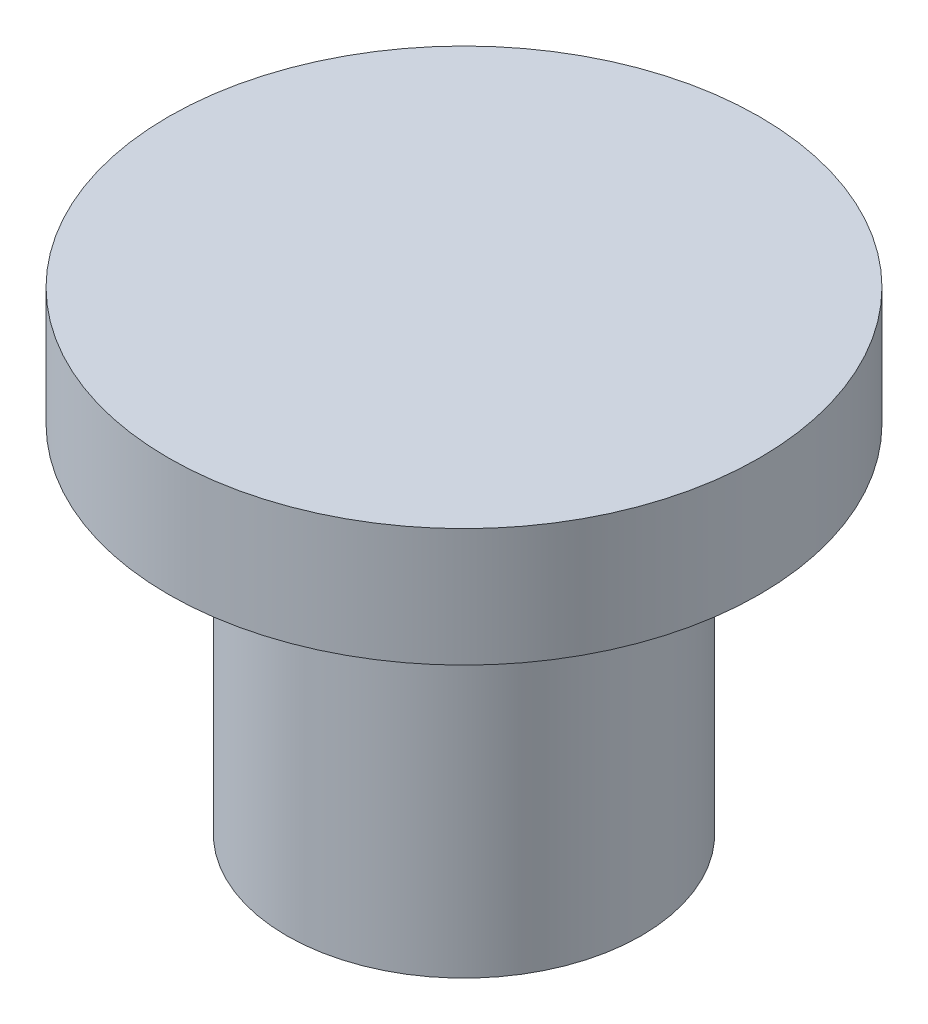
SolidWorks part; units mm, degrees
ref_plane "Спереди" through (0, 0, 0) normal (0, 0, 1) x (1, 0, 0)
ref_plane "Сверху" through (0, 0, 0) normal (0, 1, 0) x (1, 0, 0)
ref_plane "Справа" through (0, 0, 0) normal (1, 0, 0) x (0, 0, -1)
sketch "Эскиз1" plane through (0, 0, 0) normal (0, 0, 1) x (1, 0, 0)
  line L1 (-5, 8) -> (-5, 6)
  line L2 (-5, 6) -> (-3, 6)
  line L3 (-3, 6) -> (-3, 0)
  line L5 (-5, 8) -> (0, 8)
  line L7 (-3, 0) -> (0, 0)
  line L9 (0, 14.588) -> (0, -0.8473) construction
  line L10 (0, 8) -> (0, 0)
  point P8 (0, 0)
  point P10 (0, 0)
  point P11 (0, 0)
revolve "Повернуть1" add sketch "Эскиз1" angle 360 about L9
